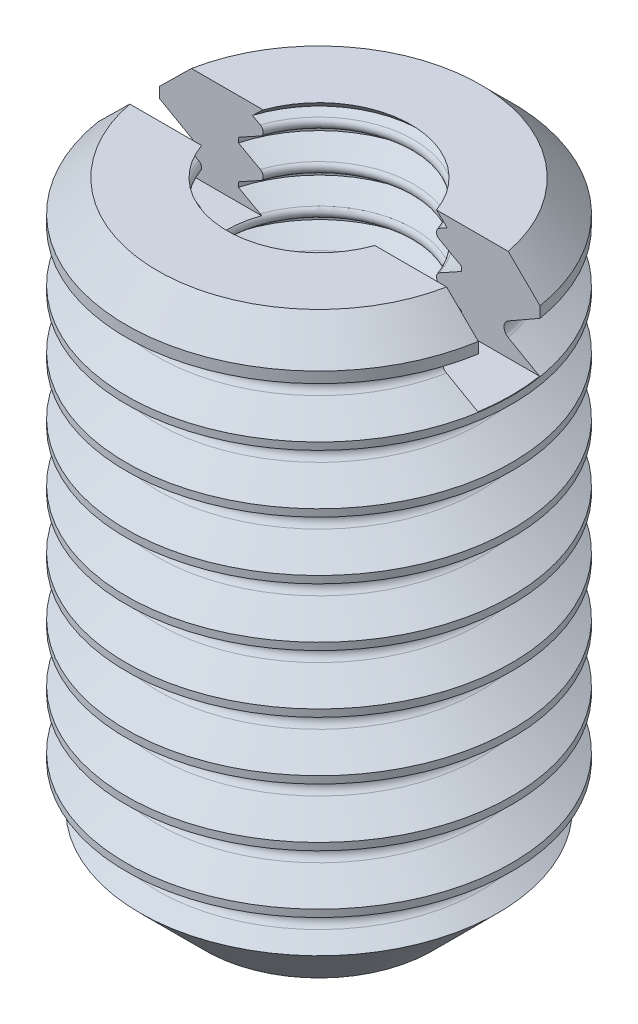
SolidWorks part; units mm, degrees
ref_plane "前视基准面" through (0, 0, 0) normal (0, 0, 1) x (1, 0, 0)
ref_plane "上视基准面" through (0, 0, 0) normal (0, 1, 0) x (1, 0, 0)
ref_plane "右视基准面" through (0, 0, 0) normal (1, 0, 0) x (0, 0, -1)
sketch "草图1" plane through (0, 0, 0) normal (0, 0, 1) x (1, 0, 0)
  line L0 (157.4083, 101.0557) -> (158.2202, 100.587)
  line L1 (158.2202, 100.587) -> (158.2202, 100.3995)
  line L2 (158.2202, 100.3995) -> (157.4083, 99.9307)
  line L3 (157.4083, 99.5557) -> (158.2202, 99.087)
  line L4 (158.2202, 99.087) -> (158.2202, 98.8995)
  line L5 (158.2202, 98.8995) -> (157.4083, 98.4307)
  line L6 (157.4083, 98.0557) -> (158.2202, 97.587)
  line L7 (158.2202, 97.587) -> (158.2202, 97.3995)
  line L8 (158.2202, 97.3995) -> (157.4083, 96.9307)
  line L9 (157.4083, 96.5557) -> (158.2202, 96.087)
  line L10 (158.2202, 96.087) -> (158.2202, 95.8995)
  line L11 (158.2202, 95.8995) -> (157.4083, 95.4307)
  line L12 (157.4083, 95.0557) -> (158.2202, 94.587)
  line L13 (158.2202, 94.587) -> (158.2202, 94.3995)
  line L14 (158.2202, 94.3995) -> (157.4083, 93.9307)
  line L15 (157.4083, 93.5557) -> (158.2202, 93.087)
  line L16 (158.2202, 93.087) -> (158.2202, 92.8995)
  line L17 (158.2202, 92.8995) -> (157.4083, 92.4307)
  line L18 (157.4083, 92.0557) -> (158.2202, 91.587)
  line L19 (158.2202, 91.587) -> (158.2202, 91.3995)
  line L20 (158.2202, 91.3995) -> (157.4083, 90.9307)
  line L21 (157.4083, 90.5557) -> (158.2202, 90.087)
  line L22 (158.2202, 90.087) -> (158.2202, 89.8995)
  line L23 (158.2202, 89.8995) -> (157.4083, 89.4307)
  line L24 (157.4083, 89.0557) -> (157.8676, 88.7906)
  line L25 (157.8676, 88.7906) -> (156.1648, 87.0877)
  line L26 (156.1648, 87.0877) -> (155.679, 87.3682)
  line L27 (155.679, 87.6182) -> (156.2202, 87.9307)
  line L28 (156.2202, 87.9307) -> (156.2202, 88.0557)
  line L29 (156.2202, 88.0557) -> (155.679, 88.3682)
  line L30 (155.679, 88.6182) -> (156.2202, 88.9307)
  line L31 (156.2202, 88.9307) -> (156.2202, 89.0557)
  line L32 (156.2202, 89.0557) -> (155.679, 89.3682)
  line L33 (155.679, 89.6182) -> (156.2202, 89.9307)
  line L34 (156.2202, 89.9307) -> (156.2202, 90.0557)
  line L35 (156.2202, 90.0557) -> (155.679, 90.3682)
  line L36 (155.679, 90.6182) -> (156.2202, 90.9307)
  line L37 (156.2202, 90.9307) -> (156.2202, 91.0557)
  line L38 (156.2202, 91.0557) -> (155.679, 91.3682)
  line L39 (155.679, 91.6182) -> (156.2202, 91.9307)
  line L40 (156.2202, 91.9307) -> (156.2202, 92.0557)
  line L41 (156.2202, 92.0557) -> (155.679, 92.3682)
  line L42 (155.679, 92.6182) -> (156.2202, 92.9307)
  line L43 (156.2202, 92.9307) -> (156.2202, 93.0557)
  line L44 (156.2202, 93.0557) -> (155.679, 93.3682)
  line L45 (155.679, 93.6182) -> (156.2202, 93.9307)
  line L46 (156.2202, 93.9307) -> (156.2202, 94.0557)
  line L47 (156.2202, 94.0557) -> (155.679, 94.3682)
  line L48 (155.679, 94.6182) -> (156.2202, 94.9307)
  line L49 (156.2202, 94.9307) -> (156.2202, 95.0557)
  line L50 (156.2202, 95.0557) -> (155.679, 95.3682)
  line L51 (155.679, 95.6182) -> (156.2202, 95.9307)
  line L52 (156.2202, 95.9307) -> (156.2202, 96.0557)
  line L53 (156.2202, 96.0557) -> (155.679, 96.3682)
  line L54 (155.679, 96.6182) -> (156.2202, 96.9307)
  line L55 (156.2202, 96.9307) -> (156.2202, 97.0557)
  line L56 (156.2202, 97.0557) -> (155.679, 97.3682)
  line L57 (155.679, 97.6182) -> (156.2202, 97.9307)
  line L58 (156.2202, 97.9307) -> (156.2202, 98.0557)
  line L59 (156.2202, 98.0557) -> (155.679, 98.3682)
  line L60 (155.679, 98.6182) -> (156.2202, 98.9307)
  line L61 (156.2202, 98.9307) -> (156.2202, 99.0557)
  line L62 (156.2202, 99.0557) -> (155.679, 99.3682)
  line L63 (155.679, 99.6182) -> (156.2202, 99.9307)
  line L64 (156.2202, 99.9307) -> (156.2202, 100.0557)
  line L65 (156.2202, 100.0557) -> (155.679, 100.3682)
  line L66 (155.679, 100.6182) -> (156.2202, 100.9307)
  line L67 (156.2202, 100.9307) -> (156.2202, 101.0557)
  line L68 (156.2202, 101.0557) -> (155.679, 101.3682)
  line L69 (155.679, 101.6182) -> (156.2202, 101.9307)
  line L70 (156.2202, 101.9307) -> (156.2202, 102.0557)
  line L71 (156.2202, 102.0557) -> (155.679, 102.3682)
  line L72 (155.679, 102.6182) -> (155.871, 102.7291)
  line L73 (155.871, 102.7291) -> (155.6068, 102.9932)
  line L74 (155.6068, 102.9932) -> (157.4082, 102.9932)
  line L75 (157.4082, 102.9932) -> (158.2202, 102.1812)
  line L76 (158.2202, 102.1812) -> (158.2202, 101.8995)
  line L77 (158.2202, 101.8995) -> (157.4083, 101.4307)
  line L78 (153.2202, 87.0877) -> (153.2202, 110.2668)
  arc A0 (157.4083, 99.9307) -> (157.4083, 99.5557) centre (157.5166, 99.7432) ccw
  arc A1 (157.4083, 98.4307) -> (157.4083, 98.0557) centre (157.5166, 98.2432) ccw
  arc A2 (157.4083, 96.9307) -> (157.4083, 96.5557) centre (157.5166, 96.7432) ccw
  arc A3 (157.4083, 95.4307) -> (157.4083, 95.0557) centre (157.5166, 95.2432) ccw
  arc A4 (157.4083, 93.9307) -> (157.4083, 93.5557) centre (157.5166, 93.7432) ccw
  arc A5 (157.4083, 92.4307) -> (157.4083, 92.0557) centre (157.5166, 92.2432) ccw
  arc A6 (157.4083, 90.9307) -> (157.4083, 90.5557) centre (157.5166, 90.7432) ccw
  arc A7 (157.4083, 89.4307) -> (157.4083, 89.0557) centre (157.5166, 89.2432) ccw
  arc A8 (155.679, 87.6182) -> (155.679, 87.3682) centre (155.7511, 87.4932) ccw
  arc A9 (155.679, 88.6182) -> (155.679, 88.3682) centre (155.7511, 88.4932) ccw
  arc A10 (155.679, 89.6182) -> (155.679, 89.3682) centre (155.7511, 89.4932) ccw
  arc A11 (155.679, 90.6182) -> (155.679, 90.3682) centre (155.7511, 90.4932) ccw
  arc A12 (155.679, 91.6182) -> (155.679, 91.3682) centre (155.7511, 91.4932) ccw
  arc A13 (155.679, 92.6182) -> (155.679, 92.3682) centre (155.7511, 92.4932) ccw
  arc A14 (155.679, 93.6182) -> (155.679, 93.3682) centre (155.7511, 93.4932) ccw
  arc A15 (155.679, 94.6182) -> (155.679, 94.3682) centre (155.7511, 94.4932) ccw
  arc A16 (155.679, 95.6182) -> (155.679, 95.3682) centre (155.7511, 95.4932) ccw
  arc A17 (155.679, 96.6182) -> (155.679, 96.3682) centre (155.7511, 96.4932) ccw
  arc A18 (155.679, 97.6182) -> (155.679, 97.3682) centre (155.7511, 97.4932) ccw
  arc A19 (155.679, 98.6182) -> (155.679, 98.3682) centre (155.7511, 98.4932) ccw
  arc A20 (155.679, 99.6182) -> (155.679, 99.3682) centre (155.7511, 99.4932) ccw
  arc A21 (155.679, 100.6182) -> (155.679, 100.3682) centre (155.7511, 100.4932) ccw
  arc A22 (155.679, 101.6182) -> (155.679, 101.3682) centre (155.7511, 101.4932) ccw
  arc A23 (155.679, 102.6182) -> (155.679, 102.3682) centre (155.7511, 102.4932) ccw
  arc A24 (157.4083, 101.4307) -> (157.4083, 101.0557) centre (157.5166, 101.2432) ccw
revolve "旋转2" add sketch "草图1" angle 360 about L78
sketch "草图2" plane through (0, 102.9932, 0) normal (0, 1, 0) x (1, 0, 0)
  line L0 (146.7202, 0.8) -> (159.7202, 0.8)
  line L1 (159.7202, 0.8) -> (159.7202, -0.8)
  line L2 (159.7202, -0.8) -> (146.7202, -0.8)
  line L3 (146.7202, -0.8) -> (146.7202, 0.8)
  dimension "D1" = 1.6
  dimension "D2" = 0.8
  dimension "D3" = 13
  dimension "D4" = 6.5
  dimension "D5" = 0.8
extrude "切除-拉伸1" cut sketch "草图2" against normal blind 2.4
